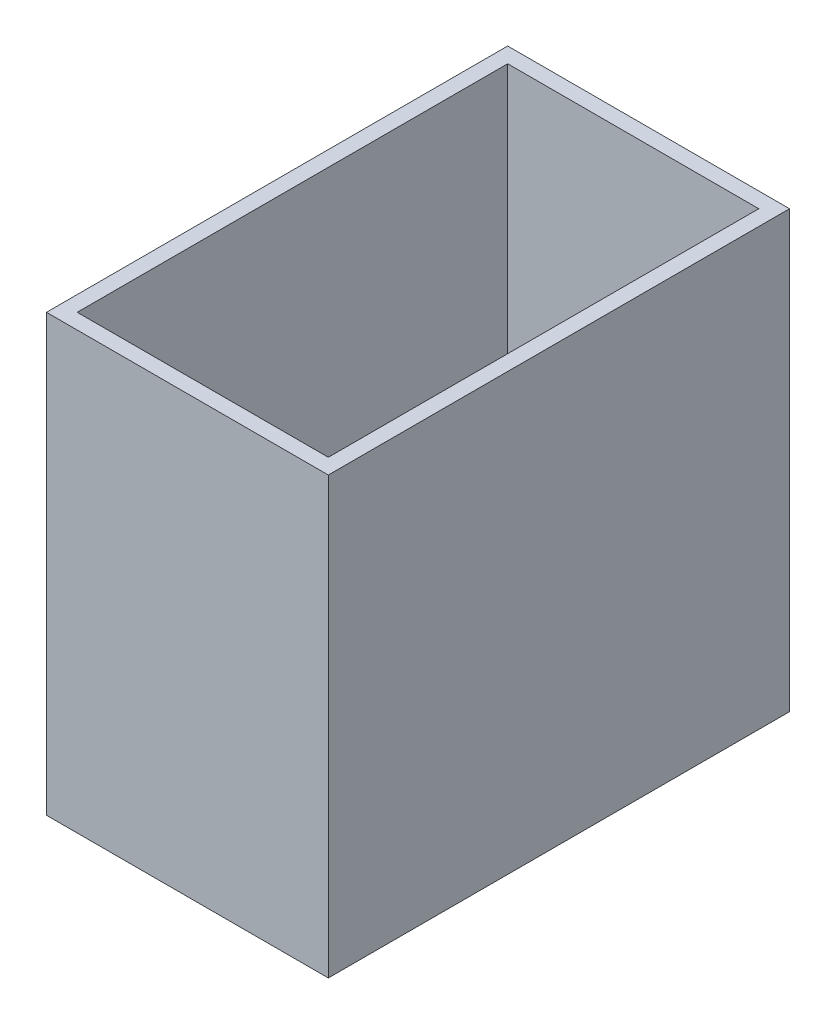
SolidWorks part; units mm, degrees
ref_plane "Front Plane" through (0, 0, 0) normal (0, 0, 1) x (1, 0, 0)
ref_plane "Top Plane" through (0, 0, 0) normal (0, 1, 0) x (1, 0, 0)
ref_plane "Right Plane" through (0, 0, 0) normal (1, 0, 0) x (0, 0, -1)
sketch "Sketch1" plane through (0, 0, 0) normal (0, 1, 0) x (1, 0, 0)
  line L1 (27.5, -45) -> (-27.5, -45)
  line L2 (27.5, -45) -> (27.5, 45)
  line L3 (27.5, 45) -> (-27.5, 45)
  line L4 (-27.5, -45) -> (-27.5, 45)
  line L5 (27.5, -45) -> (-27.5, 45) construction
  line L6 (27.5, 45) -> (-27.5, -45) construction
  point P0 (0, 0)
  dimension "D1" = 55
  dimension "D2" = 90
extrude "Boss-Extrude1" add sketch "Sketch1" along normal blind 85
shell "Shell1" thickness 3
sketch "Sketch4" plane through (0, 0, 45) normal (0, 0, 1) x (1, 0, 0)
  line L0 (-24.5, 36) -> (6.5, 3)
  line L4 (-24.5, 85) -> (-24.5, 3) construction
  line L5 (-24.5, 36) -> (-24.5, 3)
  line L6 (-24.5, 3) -> (24.5, 3) construction
  line L7 (6.5, 3) -> (-24.5, 3)
  point P0 (10.1987, 3)
  dimension "D1" = 31
  dimension "D2" = 33
extrude "Boss-Extrude4" add sketch "Sketch4" against normal up to surface (87 mm away) up to face at (0, 44, -42)
sketch "Sketch5" plane through (-27.5, 0, 0) normal (-1, 0, 0) x (0, 0, 1)
  line L1 (8, -36) -> (-8, -36)
  line L2 (8, -36) -> (8, 36)
  line L3 (8, 36) -> (-8, 36)
  line L4 (-8, -36) -> (-8, 36)
  line L5 (8, -36) -> (-8, 36) construction
  line L6 (8, 36) -> (-8, -36) construction
  point P0 (0, 0)
  dimension "D1" = 16
  dimension "D2" = 72
extrude "Cut-Extrude2" cut sketch "Sketch5" against normal blind 34
sketch "Sketch7" plane through (27.5, 0, 0) normal (1, 0, 0) x (0, 0, -1)
  line L0 (-42, 36) -> (-42, 3)
  line L1 (-42, 3) -> (-8, 3)
  line L2 (-42, 3) -> (42, 3) construction
  line L3 (-8, 0) -> (-8, 3) construction
  line L4 (-8, 3) -> (-42, 36)
  line L5 (8, 3) -> (42, 3)
  line L6 (8, 3) -> (8, 0) construction
  line L7 (42, 3) -> (42, 36)
  line L8 (42, 36) -> (8, 3)
extrude "Boss-Extrude5" add sketch "Sketch7" against normal blind 52.4
